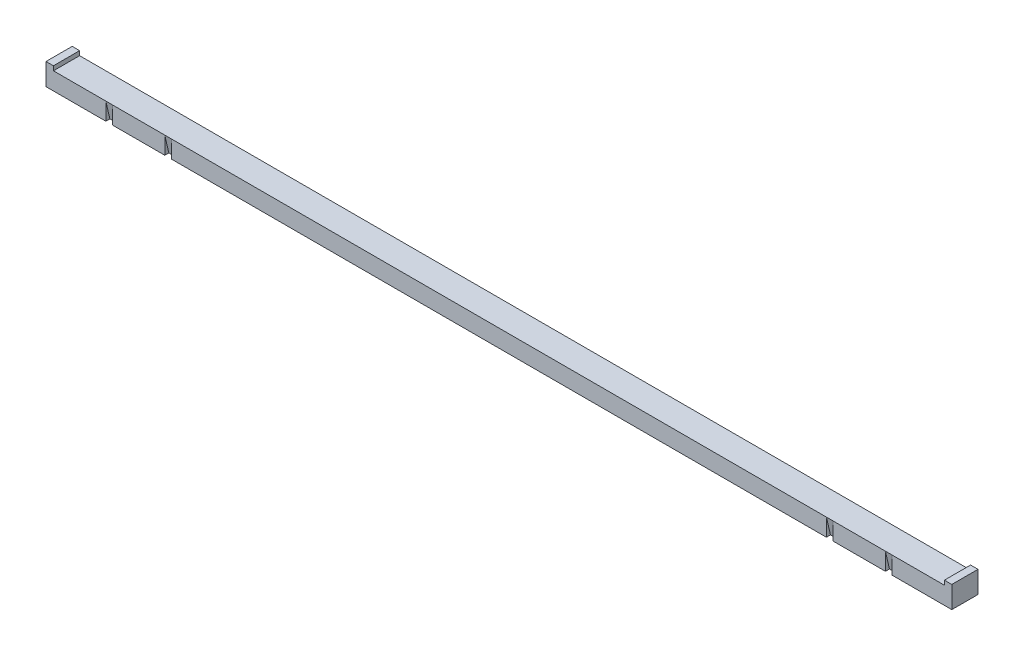
SolidWorks part; units mm, degrees
material "Polyurethane Foam Rigid"
ref_plane "Front Plane" through (0, 0, 0) normal (0, 0, 1) x (1, 0, 0)
ref_plane "Top Plane" through (0, 0, 0) normal (0, 1, 0) x (1, 0, 0)
ref_plane "Right Plane" through (0, 0, 0) normal (1, 0, 0) x (0, 0, -1)
sketch "Sketch1" plane through (0, 0, 0) normal (0, 1, 0) x (1, 0, 0)
  line L1 (-1316.99, 38.1) -> (1316.99, 38.1)
  line L2 (-1316.99, 38.1) -> (-1316.99, -38.1)
  line L3 (-1316.99, -38.1) -> (1316.99, -38.1)
  line L4 (1316.99, 38.1) -> (1316.99, -38.1)
  line L5 (-1316.99, 38.1) -> (1316.99, -38.1) construction
  line L6 (-1316.99, -38.1) -> (1316.99, 38.1) construction
  point P0 (0, 0)
  point P5 (0, 0)
  dimension "D1" = 76.2
  dimension "D2" = 2633.98
extrude "Boss-Extrude1" add sketch "Sketch1" along normal blind 50.8
sketch "Sketch2" plane through (0, 50.8, 0) normal (0, 1, 0) x (1, 0, 0)
  line L0 (-971.55, -38.1) -> (-952.5, -38.1)
  line L1 (-1143, -38.1) -> (-1123.95, -38.1)
  line L2 (-1143, -38.1) -> (-1143, -101.6)
  line L3 (-1143, -101.6) -> (-1123.95, -101.6)
  line L4 (-1123.95, -38.1) -> (-1123.95, -101.6)
  line L5 (-1143, -38.1) -> (-1123.95, -101.6) construction
  line L6 (-1143, -101.6) -> (-1123.95, -38.1) construction
  line L7 (-971.55, -38.1) -> (-971.55, -101.6)
  line L8 (-971.55, -101.6) -> (-952.5, -101.6)
  line L9 (-952.5, -38.1) -> (-952.5, -101.6)
  line L10 (-971.55, -38.1) -> (-952.5, -101.6) construction
  line L11 (-971.55, -101.6) -> (-952.5, -38.1) construction
  line L12 (-1316.99, 38.1) -> (-1316.99, -38.1) construction
  line L13 (-1316.99, -38.1) -> (1316.99, -38.1) construction
  line L14 (952.5, -38.1) -> (952.5, -101.6)
  line L15 (952.5, -38.1) -> (971.55, -38.1)
  line L16 (971.55, -38.1) -> (971.55, -101.6)
  line L17 (952.5, -101.6) -> (971.55, -101.6)
  line L18 (1123.95, -38.1) -> (1143, -38.1)
  line L19 (1143, -38.1) -> (1143, -101.6)
  line L20 (1123.95, -101.6) -> (1143, -101.6)
  line L21 (1123.95, -38.1) -> (1123.95, -101.6)
  line L22 (1316.99, -38.1) -> (1316.99, 38.1) construction
  point P0 (-1133.475, -69.85)
  point P5 (-962.025, -69.85)
  point P13 (-1143, -69.85)
  dimension "D1" = 173.99
  dimension "D2" = 19.05
  dimension "D3" = 190.5
  dimension "D4" = 19.05
  dimension "D5" = 63.5
  dimension "D7" = 173.99
  dimension "D6" = 2
revolve "Cut-Revolve4" cut sketch "Sketch2" angle 103 about axis through (-1316.99, 50.8, 38.1) along (1, 0, 0)
sketch "Sketch3" plane through (0, 50.8, 0) normal (0, 1, 0) x (1, 0, 0)
  line L0 (1316.99, -38.1) -> (1316.99, 38.1) construction
  line L1 (-1295.4, 38.1) -> (-1316.99, 38.1)
  line L2 (-1295.4, 38.1) -> (-1295.4, -38.1)
  line L3 (-1295.4, -38.1) -> (-1316.99, -38.1)
  line L4 (-1316.99, 38.1) -> (-1316.99, -38.1)
  line L5 (-1295.4, 38.1) -> (-1316.99, -38.1) construction
  line L6 (-1295.4, -38.1) -> (-1316.99, 38.1) construction
  line L7 (1295.4, 38.1) -> (1316.99, 38.1)
  line L8 (1295.4, 38.1) -> (1295.4, -38.1)
  line L9 (1295.4, -38.1) -> (1316.99, -38.1)
  line L10 (1316.99, 38.1) -> (1316.99, -38.1)
  line L11 (1295.4, 38.1) -> (1316.99, -38.1) construction
  line L12 (1295.4, -38.1) -> (1316.99, 38.1) construction
  line L13 (1316.99, 38.1) -> (-1316.99, 38.1) construction
  point P0 (-1306.195, 0)
  point P6 (1295.4, 38.1)
  point P8 (1306.195, 0)
  dimension "D1" = 21.59
  dimension "D2" = 21.59
extrude "Boss-Extrude2" add sketch "Sketch3" along normal blind 12.7
